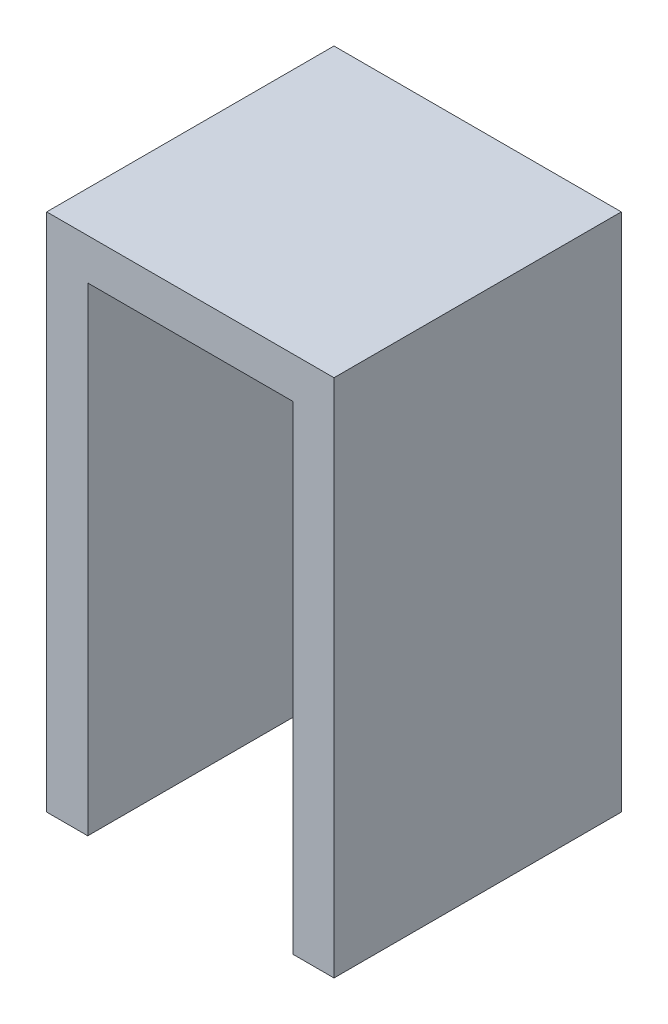
SolidWorks part; units mm, degrees
ref_plane "前基準面" through (0, 0, 0) normal (0, 0, 1) x (1, 0, 0)
ref_plane "上基準面" through (0, 0, 0) normal (0, 1, 0) x (1, 0, 0)
ref_plane "右基準面" through (0, 0, 0) normal (1, 0, 0) x (0, 0, -1)
sketch "草圖1" plane through (0, 0, 0) normal (0, 0, 1) x (1, 0, 0)
  line L1 (-7.9981, 8.3166) -> (7.0019, 8.3166)
  line L2 (-7.9981, 8.3166) -> (-7.9981, -23.6834)
  line L3 (-7.9981, -23.6834) -> (7.0019, -23.6834)
  line L4 (7.0019, 8.3166) -> (7.0019, -23.6834)
  line L5 (-10.9981, 11.3166) -> (10.0019, 11.3166)
  line L6 (-10.9981, 11.3166) -> (-10.9981, -26.6834)
  line L7 (-10.9981, -26.6834) -> (10.0019, -26.6834)
  line L8 (10.0019, 11.3166) -> (10.0019, -26.6834)
  dimension "D1" = 15
  dimension "D2" = 32
  dimension "D3" = 3
  dimension "D4" = 3
  dimension "D5" = 3
  dimension "D6" = 3
extrude "填料-伸長1" add sketch "草圖1" along normal blind 18
sketch "草圖2" plane through (0, 0, 0) normal (0, 0, -1) x (-1, 0, 0)
  line L1 (-10.0019, 11.3166) -> (10.9981, 11.3166)
  line L2 (-10.0019, 11.3166) -> (-10.0019, -26.6834)
  line L3 (-10.0019, -26.6834) -> (10.9981, -26.6834)
  line L4 (10.9981, 11.3166) -> (10.9981, -26.6834)
extrude "填料-伸長2" add sketch "草圖2" along normal blind 3
sketch "草圖3" plane through (0, -26.6834, 0) normal (0, -1, 0) x (1, 0, 0)
  line L0 (-10.9981, 18) -> (10.0019, 18) construction
  line L1 (-7.9981, 18) -> (7.0019, 18)
  line L2 (-7.9981, 18) -> (-7.9981, 3)
  line L3 (-7.9981, 3) -> (7.0019, 3)
  line L4 (7.0019, 18) -> (7.0019, 3)
  line L5 (-10.9981, 18) -> (-10.9981, -3) construction
  line L6 (10.0019, 18) -> (10.0019, -3) construction
  line L7 (10.0019, -3) -> (-10.9981, -3) construction
  dimension "D1" = 3
  dimension "D2" = 3
  dimension "D3" = 6
extrude "除料-伸長1" cut sketch "草圖3" against normal blind 3
